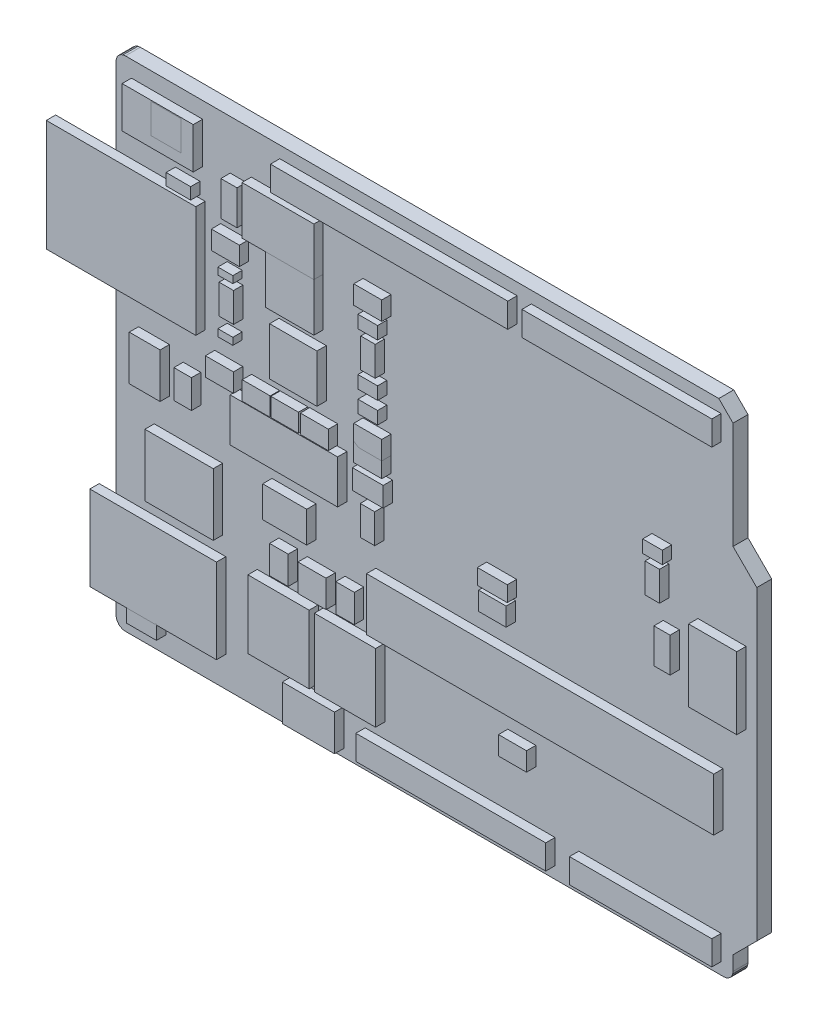
SolidWorks part; units mm, degrees
ref_plane "Front Plane" through (0, 0, 0) normal (0, 0, 1) x (1, 0, 0)
ref_plane "Top Plane" through (0, 0, 0) normal (0, 1, 0) x (1, 0, 0)
ref_plane "Right Plane" through (0, 0, 0) normal (1, 0, 0) x (0, 0, -1)
sketch "Sketch1" plane through (0, 0, 0) normal (0, 0, 1) x (1, 0, 0)
  line L0 (64.516, 53.34) -> (66.04, 51.816)
  line L1 (66.04, 51.816) -> (66.04, 40.386)
  line L2 (66.04, 40.386) -> (68.58, 37.846)
  line L3 (68.58, 37.846) -> (68.58, 5.08)
  line L4 (68.58, 5.08) -> (66.04, 2.54)
  line L5 (66.04, 2.54) -> (66.04, 1)
  line L6 (66.04, 1) -> (66.0059, 0.7412)
  line L7 (66.0059, 0.7412) -> (65.906, 0.5)
  line L8 (65.906, 0.5) -> (65.7471, 0.2929)
  line L9 (65.7471, 0.2929) -> (65.54, 0.134)
  line L10 (65.54, 0.134) -> (65.2988, 0.0341)
  line L11 (65.2988, 0.0341) -> (65.04, 0)
  line L12 (65.04, 0) -> (1, 0)
  line L13 (1, 0) -> (0.7412, 0.0341)
  line L14 (0.7412, 0.0341) -> (0.5, 0.134)
  line L15 (0.5, 0.134) -> (0.2929, 0.2929)
  line L16 (0.2929, 0.2929) -> (0.134, 0.5)
  line L17 (0.134, 0.5) -> (0.0341, 0.7412)
  line L18 (0.0341, 0.7412) -> (0, 1)
  line L19 (0, 1) -> (0, 52.34)
  line L20 (0, 52.34) -> (0.0341, 52.5988)
  line L21 (0.0341, 52.5988) -> (0.134, 52.84)
  line L22 (0.134, 52.84) -> (0.2929, 53.0471)
  line L23 (0.2929, 53.0471) -> (0.5, 53.206)
  line L24 (0.5, 53.206) -> (0.7412, 53.3059)
  line L25 (0.7412, 53.3059) -> (1, 53.34)
  line L26 (1, 53.34) -> (64.516, 53.34)
extrude "BOARD" add sketch "Sketch1" along normal blind 1.6 separate body
ref_plane "Plane4" through (0, 0, 1.6) normal (0, 0, 1) x (1, 0, 0)
sketch "Sketch2" plane through (0, 0, 1.6) normal (0, 0, 1) x (1, 0, 0)
  line L0 (49.53, 3.8862) -> (64.77, 3.8862)
  line L1 (64.77, 3.8862) -> (64.77, 1.27)
  line L2 (64.77, 1.27) -> (49.53, 1.27)
  line L3 (49.53, 1.27) -> (49.53, 3.8862)
extrude "1X06-1" add sketch "Sketch2" along normal blind 1 separate body
sketch "Sketch3" plane through (0, 0, 1.6) normal (0, 0, 1) x (1, 0, 0)
  line L0 (19.4234, 16.8654) -> (19.4234, 13.8686)
  line L1 (19.4234, 13.8686) -> (17.432, 13.8686)
  line L2 (17.432, 13.8686) -> (17.432, 16.8654)
  line L3 (17.432, 16.8654) -> (19.4234, 16.8654)
extrude "C0603-ROUND-1" add sketch "Sketch3" along normal blind 1 separate body
sketch "Sketch4" plane through (0, 0, 1.6) normal (0, 0, 1) x (1, 0, 0)
  line L0 (13.5634, 28.8366) -> (10.5666, 28.8366)
  line L1 (10.5666, 28.8366) -> (10.5666, 30.828)
  line L2 (10.5666, 30.828) -> (13.5634, 30.828)
  line L3 (13.5634, 30.828) -> (13.5634, 28.8366)
extrude "C0603-ROUND-2" add sketch "Sketch4" along normal blind 1 separate body
sketch "Sketch5" plane through (0, 0, 1.6) normal (0, 0, 1) x (1, 0, 0)
  line L0 (24.5186, 13.8686) -> (24.5186, 16.8654)
  line L1 (24.5186, 16.8654) -> (26.51, 16.8654)
  line L2 (26.51, 16.8654) -> (26.51, 13.8686)
  line L3 (26.51, 13.8686) -> (24.5186, 13.8686)
extrude "C0603-ROUND-3" add sketch "Sketch5" along normal blind 1 separate body
sketch "Sketch6" plane through (0, 0, 1.6) normal (0, 0, 1) x (1, 0, 0)
  line L0 (29.4384, 43.4416) -> (26.4416, 43.4416)
  line L1 (26.4416, 43.4416) -> (26.4416, 45.433)
  line L2 (26.4416, 45.433) -> (29.4384, 45.433)
  line L3 (29.4384, 45.433) -> (29.4384, 43.4416)
extrude "C0603-ROUND-4" add sketch "Sketch6" along normal blind 1 separate body
sketch "Sketch7" plane through (0, 0, 1.6) normal (0, 0, 1) x (1, 0, 0)
  line L0 (26.4416, 30.8534) -> (29.4384, 30.8534)
  line L1 (29.4384, 30.8534) -> (29.4384, 28.862)
  line L2 (29.4384, 28.862) -> (26.4416, 28.862)
  line L3 (26.4416, 28.862) -> (26.4416, 30.8534)
extrude "C0603-ROUND-5" add sketch "Sketch7" along normal blind 1 separate body
sketch "Sketch8" plane through (0, 0, 1.6) normal (0, 0, 1) x (1, 0, 0)
  line L0 (44.9324, 9.4056) -> (41.9356, 9.4056)
  line L1 (41.9356, 9.4056) -> (41.9356, 11.397)
  line L2 (41.9356, 11.397) -> (44.9324, 11.397)
  line L3 (44.9324, 11.397) -> (44.9324, 9.4056)
extrude "C0603-ROUND-6" add sketch "Sketch8" along normal blind 1 separate body
sketch "Sketch9" plane through (0, 0, 1.6) normal (0, 0, 1) x (1, 0, 0)
  line L0 (26.4416, 32.5044) -> (29.4384, 32.5044)
  line L1 (29.4384, 32.5044) -> (29.4384, 30.513)
  line L2 (29.4384, 30.513) -> (26.4416, 30.513)
  line L3 (26.4416, 30.513) -> (26.4416, 32.5044)
extrude "C0603-ROUND-7" add sketch "Sketch9" along normal blind 1 separate body
sketch "Sketch10" plane through (0, 0, 1.6) normal (0, 0, 1) x (1, 0, 0)
  line L0 (14.1984, 40.9016) -> (11.2016, 40.9016)
  line L1 (11.2016, 40.9016) -> (11.2016, 42.893)
  line L2 (11.2016, 42.893) -> (14.1984, 42.893)
  line L3 (14.1984, 42.893) -> (14.1984, 40.9016)
extrude "C0603-ROUND-8" add sketch "Sketch10" along normal blind 1 separate body
sketch "Sketch11" plane through (0, 0, 1.6) normal (0, 0, 1) x (1, 0, 0)
  line L0 (17.5004, 28.5826) -> (14.5036, 28.5826)
  line L1 (14.5036, 28.5826) -> (14.5036, 30.574)
  line L2 (14.5036, 30.574) -> (17.5004, 30.574)
  line L3 (17.5004, 30.574) -> (17.5004, 28.5826)
extrude "C0603-ROUND-9" add sketch "Sketch11" along normal blind 1 separate body
sketch "Sketch12" plane through (0, 0, 1.6) normal (0, 0, 1) x (1, 0, 0)
  line L0 (20.7266, 30.5994) -> (23.7234, 30.5994)
  line L1 (23.7234, 30.5994) -> (23.7234, 28.608)
  line L2 (23.7234, 28.608) -> (20.7266, 28.608)
  line L3 (20.7266, 28.608) -> (20.7266, 30.5994)
extrude "C0603-ROUND-10" add sketch "Sketch12" along normal blind 1 separate body
sketch "Sketch13" plane through (0, 0, 1.6) normal (0, 0, 1) x (1, 0, 0)
  line L0 (24.384, 0.8382) -> (18.796, 0.8382)
  line L1 (18.796, 0.8382) -> (18.796, 4.699)
  line L2 (18.796, 4.699) -> (24.384, 4.699)
  line L3 (24.384, 4.699) -> (24.384, 0.8382)
extrude "SMB-1" add sketch "Sketch13" along normal blind 1 separate body
sketch "Sketch14" plane through (0, 0, 1.6) normal (0, 0, 1) x (1, 0, 0)
  line L0 (60.2996, 29.7942) -> (60.2996, 26.0858)
  line L1 (60.2996, 26.0858) -> (58.5724, 26.0858)
  line L2 (58.5724, 26.0858) -> (58.5724, 29.7942)
  line L3 (58.5724, 29.7942) -> (60.2996, 29.7942)
extrude "MINIMELF-1" add sketch "Sketch14" along normal blind 1 separate body
sketch "Sketch15" plane through (0, 0, 1.6) normal (0, 0, 1) x (1, 0, 0)
  line L0 (12.2174, 44.3738) -> (12.2174, 48.0822)
  line L1 (12.2174, 48.0822) -> (13.9446, 48.0822)
  line L2 (13.9446, 48.0822) -> (13.9446, 44.3738)
  line L3 (13.9446, 44.3738) -> (12.2174, 44.3738)
extrude "MINIMELF-2" add sketch "Sketch15" along normal blind 1 separate body
sketch "Sketch16" plane through (0, 0, 1.6) normal (0, 0, 1) x (1, 0, 0)
  line L0 (2.413, 24.1554) -> (2.413, 28.9408)
  line L1 (2.413, 28.9408) -> (5.715, 28.9408)
  line L2 (5.715, 28.9408) -> (5.715, 24.1554)
  line L3 (5.715, 24.1554) -> (2.413, 24.1554)
extrude "L1812-1" add sketch "Sketch16" along normal blind 1 separate body
sketch "Sketch17" plane through (0, 0, 1.6) normal (0, 0, 1) x (1, 0, 0)
  line L0 (4.7578, 51.5032) -> (7.9422, 51.5032)
  line L1 (7.9422, 51.5032) -> (7.9422, 48.3188)
  line L2 (7.9422, 48.3188) -> (4.7578, 48.3188)
  line L3 (4.7578, 48.3188) -> (4.7578, 51.5032)
extrude "FIDUCIA-MOUNT-1" add sketch "Sketch17" along normal blind 1 separate body
sketch "Sketch18" plane through (0, 0, 1.6) normal (0, 0, 1) x (1, 0, 0)
  line L0 (52.2478, 18.3332) -> (55.4322, 18.3332)
  line L1 (55.4322, 18.3332) -> (55.4322, 15.1488)
  line L2 (55.4322, 15.1488) -> (52.2478, 15.1488)
  line L3 (52.2478, 15.1488) -> (52.2478, 18.3332)
extrude "FIDUCIA-MOUNT-2" add sketch "Sketch18" along normal blind 1 separate body
sketch "Sketch19" plane through (0, 0, 1.6) normal (0, 0, 1) x (1, 0, 0)
  line L0 (2.1378, 5.0022) -> (5.3222, 5.0022)
  line L1 (5.3222, 5.0022) -> (5.3222, 1.8178)
  line L2 (5.3222, 1.8178) -> (2.1378, 1.8178)
  line L3 (2.1378, 1.8178) -> (2.1378, 5.0022)
extrude "FIDUCIA-MOUNT-3" add sketch "Sketch19" along normal blind 1 separate body
sketch "Sketch20" plane through (0, 0, 0) normal (0, 0, 1) x (1, 0, 0)
  line L0 (13.081, 41.656) -> (9.779, 41.656)
  line L1 (9.779, 41.656) -> (9.779, 39.5478)
  line L2 (9.779, 39.5478) -> (13.081, 39.5478)
  line L3 (13.081, 39.5478) -> (13.081, 41.656)
extrude "SJ-1" add sketch "Sketch20" against normal blind 1 separate body
sketch "Sketch21" plane through (0, 0, 1.6) normal (0, 0, 1) x (1, 0, 0)
  line L0 (67.437, 31.8262) -> (67.437, 24.13)
  line L1 (67.437, 24.13) -> (62.2808, 24.13)
  line L2 (62.2808, 24.13) -> (62.2808, 31.8262)
  line L3 (62.2808, 31.8262) -> (67.437, 31.8262)
extrude "2X03-1" add sketch "Sketch21" along normal blind 1 separate body
sketch "Sketch22" plane through (0, 0, 1.6) normal (0, 0, 1) x (1, 0, 0)
  line L0 (22.1742, 43.688) -> (14.478, 43.688)
  line L1 (14.478, 43.688) -> (14.478, 48.8442)
  line L2 (14.478, 48.8442) -> (22.1742, 48.8442)
  line L3 (22.1742, 48.8442) -> (22.1742, 43.688)
extrude "2X03-2" add sketch "Sketch22" along normal blind 1 separate body
sketch "Sketch23" plane through (0, 0, 1.6) normal (0, 0, 1) x (1, 0, 0)
  line L0 (42.926, 49.4538) -> (17.526, 49.4538)
  line L1 (17.526, 49.4538) -> (17.526, 52.07)
  line L2 (17.526, 52.07) -> (42.926, 52.07)
  line L3 (42.926, 52.07) -> (42.926, 49.4538)
extrude "1X10-1" add sketch "Sketch23" along normal blind 1 separate body
sketch "Sketch24" plane through (0, 0, 1.6) normal (0, 0, 1) x (1, 0, 0)
  line L0 (64.77, 49.4538) -> (44.45, 49.4538)
  line L1 (44.45, 49.4538) -> (44.45, 52.07)
  line L2 (44.45, 52.07) -> (64.77, 52.07)
  line L3 (64.77, 52.07) -> (64.77, 49.4538)
extrude "1X08-1" add sketch "Sketch24" along normal blind 1 separate body
sketch "Sketch25" plane through (0, 0, 1.6) normal (0, 0, 1) x (1, 0, 0)
  line L0 (26.67, 3.8862) -> (46.99, 3.8862)
  line L1 (46.99, 3.8862) -> (46.99, 1.27)
  line L2 (46.99, 1.27) -> (26.67, 1.27)
  line L3 (26.67, 1.27) -> (26.67, 3.8862)
extrude "1X08-2" add sketch "Sketch25" along normal blind 1 separate body
sketch "Sketch26" plane through (0, 0, 1.6) normal (0, 0, 1) x (1, 0, 0)
  line L0 (17.018, 38.5318) -> (17.018, 43.688)
  line L1 (17.018, 43.688) -> (22.1742, 43.688)
  line L2 (22.1742, 43.688) -> (22.1742, 38.5318)
  line L3 (22.1742, 38.5318) -> (17.018, 38.5318)
extrude "2X02-1" add sketch "Sketch26" along normal blind 1 separate body
sketch "Sketch27" plane through (0, 0, 1.6) normal (0, 0, 1) x (1, 0, 0)
  line L0 (28.99, 42.8398) -> (28.99, 41.489)
  line L1 (28.99, 41.489) -> (26.89, 41.489)
  line L2 (26.89, 41.489) -> (26.89, 42.8398)
  line L3 (26.89, 42.8398) -> (28.99, 42.8398)
extrude "CHIP-LED0805-1" add sketch "Sketch27" along normal blind 1 separate body
sketch "Sketch28" plane through (0, 0, 1.6) normal (0, 0, 1) x (1, 0, 0)
  line L0 (59.47, 37.2518) -> (59.47, 35.901)
  line L1 (59.47, 35.901) -> (57.37, 35.901)
  line L2 (57.37, 35.901) -> (57.37, 37.2518)
  line L3 (57.37, 37.2518) -> (59.47, 37.2518)
extrude "CHIP-LED0805-2" add sketch "Sketch28" along normal blind 1 separate body
sketch "Sketch29" plane through (0, 0, 1.6) normal (0, 0, 1) x (1, 0, 0)
  line L0 (26.89, 33.6142) -> (26.89, 34.965)
  line L1 (26.89, 34.965) -> (28.99, 34.965)
  line L2 (28.99, 34.965) -> (28.99, 33.6142)
  line L3 (28.99, 33.6142) -> (26.89, 33.6142)
extrude "CHIP-LED0805-3" add sketch "Sketch29" along normal blind 1 separate body
sketch "Sketch30" plane through (0, 0, 1.6) normal (0, 0, 1) x (1, 0, 0)
  line L0 (26.89, 35.9002) -> (26.89, 37.251)
  line L1 (26.89, 37.251) -> (28.99, 37.251)
  line L2 (28.99, 37.251) -> (28.99, 35.9002)
  line L3 (28.99, 35.9002) -> (26.89, 35.9002)
extrude "CHIP-LED0805-4" add sketch "Sketch30" along normal blind 1 separate body
sketch "Sketch31" plane through (0, 0, 1.6) normal (0, 0, 1) x (1, 0, 0)
  line L0 (8.9835, 44.46) -> (6.3565, 44.46)
  line L1 (6.3565, 44.46) -> (6.3565, 45.71)
  line L2 (6.3565, 45.71) -> (8.9835, 45.71)
  line L3 (8.9835, 45.71) -> (8.9835, 44.46)
extrude "0805-1" add sketch "Sketch31" along normal blind 1 separate body
sketch "Sketch32" plane through (0, 0, 1.6) normal (0, 0, 1) x (1, 0, 0)
  line L0 (22.2262, 5.494) -> (22.2262, 12.794)
  line L1 (22.2262, 12.794) -> (28.777, 12.794)
  line L2 (28.777, 12.794) -> (28.777, 5.494)
  line L3 (28.777, 5.494) -> (22.2262, 5.494)
extrude "PANASONIC_D-1" add sketch "Sketch32" along normal blind 1 separate body
sketch "Sketch33" plane through (0, 0, 1.6) normal (0, 0, 1) x (1, 0, 0)
  line L0 (15.1142, 5.494) -> (15.1142, 12.794)
  line L1 (15.1142, 12.794) -> (21.665, 12.794)
  line L2 (21.665, 12.794) -> (21.665, 5.494)
  line L3 (21.665, 5.494) -> (15.1142, 5.494)
extrude "PANASONIC_D-2" add sketch "Sketch33" along normal blind 1 separate body
sketch "Sketch34" plane through (0, 0, 1.6) normal (0, 0, 1) x (1, 0, 0)
  line L0 (17.577, 30.574) -> (20.523, 30.574)
  line L1 (20.523, 30.574) -> (20.523, 28.608)
  line L2 (20.523, 28.608) -> (17.577, 28.608)
  line L3 (17.577, 28.608) -> (17.577, 30.574)
extrude "R0603-ROUND-1" add sketch "Sketch34" along normal blind 1 separate body
sketch "Sketch35" plane through (0, 0, 1.6) normal (0, 0, 1) x (1, 0, 0)
  line L0 (42.748, 21.75) -> (39.802, 21.75)
  line L1 (39.802, 21.75) -> (39.802, 23.716)
  line L2 (39.802, 23.716) -> (42.748, 23.716)
  line L3 (42.748, 23.716) -> (42.748, 21.75)
extrude "R0603-ROUND-2" add sketch "Sketch35" along normal blind 1 separate body
sketch "Sketch36" plane through (0, 0, 1.6) normal (0, 0, 1) x (1, 0, 0)
  line L0 (1.651, 51.603) -> (9.2635, 51.603)
  line L1 (9.2635, 51.603) -> (9.2635, 47.203)
  line L2 (9.2635, 47.203) -> (1.651, 47.203)
  line L3 (1.651, 47.203) -> (1.651, 51.603)
extrude "TS42-1" add sketch "Sketch36" along normal blind 1 separate body
sketch "Sketch37" plane through (0, 0, 1.6) normal (0, 0, 1) x (1, 0, 0)
  line L0 (26.289, 28.321) -> (29.591, 28.321)
  line L1 (29.591, 28.321) -> (29.591, 26.2128)
  line L2 (29.591, 26.2128) -> (26.289, 26.2128)
  line L3 (26.289, 26.2128) -> (26.289, 28.321)
extrude "SJ-2" add sketch "Sketch37" along normal blind 1 separate body
sketch "Sketch38" plane through (0, 0, 1.6) normal (0, 0, 1) x (1, 0, 0)
  line L0 (27.1392, 22.2752) -> (27.1392, 25.426)
  line L1 (27.1392, 25.426) -> (28.69, 25.426)
  line L2 (28.69, 25.426) -> (28.69, 22.2752)
  line L3 (28.69, 22.2752) -> (27.1392, 22.2752)
extrude "CAY16-1" add sketch "Sketch38" along normal blind 1 separate body
sketch "Sketch39" plane through (0, 0, 1.6) normal (0, 0, 1) x (1, 0, 0)
  line L0 (28.7408, 40.9708) -> (28.7408, 37.82)
  line L1 (28.7408, 37.82) -> (27.19, 37.82)
  line L2 (27.19, 37.82) -> (27.19, 40.9708)
  line L3 (27.19, 40.9708) -> (28.7408, 40.9708)
extrude "CAY16-2" add sketch "Sketch39" along normal blind 1 separate body
sketch "Sketch40" plane through (0, 0, 1.6) normal (0, 0, 1) x (1, 0, 0)
  line L0 (12.0262, 35.2292) -> (12.0262, 38.38)
  line L1 (12.0262, 38.38) -> (13.577, 38.38)
  line L2 (13.577, 38.38) -> (13.577, 35.2292)
  line L3 (13.577, 35.2292) -> (12.0262, 35.2292)
extrude "CAY16-3" add sketch "Sketch40" along normal blind 1 separate body
sketch "Sketch41" plane through (0, 0, 1.6) normal (0, 0, 1) x (1, 0, 0)
  line L0 (57.6192, 32.1812) -> (57.6192, 35.332)
  line L1 (57.6192, 35.332) -> (59.17, 35.332)
  line L2 (59.17, 35.332) -> (59.17, 32.1812)
  line L3 (59.17, 32.1812) -> (57.6192, 32.1812)
extrude "CAY16-4" add sketch "Sketch41" along normal blind 1 separate body
sketch "Sketch42" plane through (0, 0, 1.6) normal (0, 0, 1) x (1, 0, 0)
  line L0 (9.0678, 28.0416) -> (9.0678, 24.9936)
  line L1 (9.0678, 24.9936) -> (7.1882, 24.9936)
  line L2 (7.1882, 24.9936) -> (7.1882, 28.0416)
  line L3 (7.1882, 28.0416) -> (9.0678, 28.0416)
extrude "SOT-23-1" add sketch "Sketch42" along normal blind 1 separate body
sketch "Sketch43" plane through (0, 0, 1.6) normal (0, 0, 1) x (1, 0, 0)
  line L0 (-19.193, -24.368) -> (-21.193, -24.368)
  line L1 (-21.193, -24.368) -> (-21.193, -22.368)
  line L2 (-21.193, -22.368) -> (-19.193, -22.368)
  line L3 (-19.193, -22.368) -> (-19.193, -24.368)
sketch "Sketch44" plane through (0, 0, 1.6) normal (0, 0, 1) x (1, 0, 0)
  line L0 (4.0894, 14.1224) -> (4.0894, 20.7772)
  line L1 (4.0894, 20.7772) -> (11.4046, 20.7772)
  line L2 (11.4046, 20.7772) -> (11.4046, 14.1224)
  line L3 (11.4046, 14.1224) -> (4.0894, 14.1224)
extrude "SOT223-1" add sketch "Sketch44" along normal blind 1 separate body
sketch "Sketch45" plane through (0, 0, 1.6) normal (0, 0, 1) x (1, 0, 0)
  line L0 (23.471, 16.662) -> (23.471, 13.7418)
  line L1 (23.471, 13.7418) -> (20.471, 13.7418)
  line L2 (20.471, 13.7418) -> (20.471, 16.662)
  line L3 (20.471, 16.662) -> (23.471, 16.662)
extrude "SOT23-DBV-1" add sketch "Sketch45" along normal blind 1 separate body
sketch "Sketch46" plane through (0, 0, 1.6) normal (0, 0, 1) x (1, 0, 0)
  line L0 (17.439, 32.1075) -> (17.439, 37.2345)
  line L1 (17.439, 37.2345) -> (22.5025, 37.2345)
  line L2 (22.5025, 37.2345) -> (22.5025, 32.1075)
  line L3 (22.5025, 32.1075) -> (17.439, 32.1075)
extrude "MLF32-1" add sketch "Sketch46" along normal blind 1 separate body
sketch "Sketch47" plane through (0, 0, 1.6) normal (0, 0, 1) x (1, 0, 0)
  line L0 (16.6943, 18.694) -> (16.6943, 22.0202)
  line L1 (16.6943, 22.0202) -> (21.4069, 22.0202)
  line L2 (21.4069, 22.0202) -> (21.4069, 18.694)
  line L3 (21.4069, 18.694) -> (16.6943, 18.694)
extrude "MSOP08-1" add sketch "Sketch47" along normal blind 1 separate body
sketch "Sketch48" plane through (0, 0, 1.6) normal (0, 0, 1) x (1, 0, 0)
  line L0 (-1.8034, 3.2385) -> (-1.8034, 12.2936)
  line L1 (-1.8034, 12.2936) -> (11.7475, 12.2936)
  line L2 (11.7475, 12.2936) -> (11.7475, 3.2385)
  line L3 (11.7475, 3.2385) -> (-1.8034, 3.2385)
extrude "POWERSUPPLY_DC-21MM-1" add sketch "Sketch48" along normal blind 1 separate body
sketch "Sketch49" plane through (0, 0, 1.6) normal (0, 0, 1) x (1, 0, 0)
  line L0 (9.537, 44.127) -> (9.537, 32.2)
  line L1 (9.537, 32.2) -> (-6.467, 32.2)
  line L2 (-6.467, 32.2) -> (-6.467, 44.127)
  line L3 (-6.467, 44.127) -> (9.537, 44.127)
extrude "PN61729-1" add sketch "Sketch49" along normal blind 1 separate body
sketch "Sketch50" plane through (0, 0, 1.6) normal (0, 0, 1) x (1, 0, 0)
  line L0 (24.7142, 23.876) -> (13.208, 23.876)
  line L1 (13.208, 23.876) -> (13.208, 28.5242)
  line L2 (13.208, 28.5242) -> (24.7142, 28.5242)
  line L3 (24.7142, 28.5242) -> (24.7142, 23.876)
extrude "QS-1" add sketch "Sketch50" along normal blind 1 separate body
sketch "Sketch51" plane through (0, 0, 1.6) normal (0, 0, 1) x (1, 0, 0)
  line L0 (39.675, 25.7555) -> (42.875, 25.7555)
  line L1 (42.875, 25.7555) -> (42.875, 24.092)
  line L2 (42.875, 24.092) -> (39.675, 24.092)
  line L3 (39.675, 24.092) -> (39.675, 25.7555)
extrude "RESONATOR-1" add sketch "Sketch51" along normal blind 1 separate body
sketch "Sketch52" plane through (0, 0, 1.6) normal (0, 0, 1) x (1, 0, 0)
  line L0 (13.5008, 38.9692) -> (11.8992, 38.9692)
  line L1 (11.8992, 38.9692) -> (11.8992, 39.72)
  line L2 (11.8992, 39.72) -> (13.5008, 39.72)
  line L3 (13.5008, 39.72) -> (13.5008, 38.9692)
extrude "CT_CN0603-1" add sketch "Sketch52" along normal blind 1 separate body
sketch "Sketch53" plane through (0, 0, 1.6) normal (0, 0, 1) x (1, 0, 0)
  line L0 (13.5008, 33.2542) -> (11.8992, 33.2542)
  line L1 (11.8992, 33.2542) -> (11.8992, 34.005)
  line L2 (11.8992, 34.005) -> (13.5008, 34.005)
  line L3 (13.5008, 34.005) -> (13.5008, 33.2542)
extrude "CT_CN0603-2" add sketch "Sketch53" along normal blind 1 separate body
sketch "Sketch54" plane through (0, 0, 1.6) normal (0, 0, 1) x (1, 0, 0)
  line L0 (64.9732, 13.589) -> (27.813, 13.589)
  line L1 (27.813, 13.589) -> (27.813, 19.2532)
  line L2 (27.813, 19.2532) -> (64.9732, 19.2532)
  line L3 (64.9732, 19.2532) -> (64.9732, 13.589)
extrude "DIL28-3-1" add sketch "Sketch54" along normal blind 1 separate body
